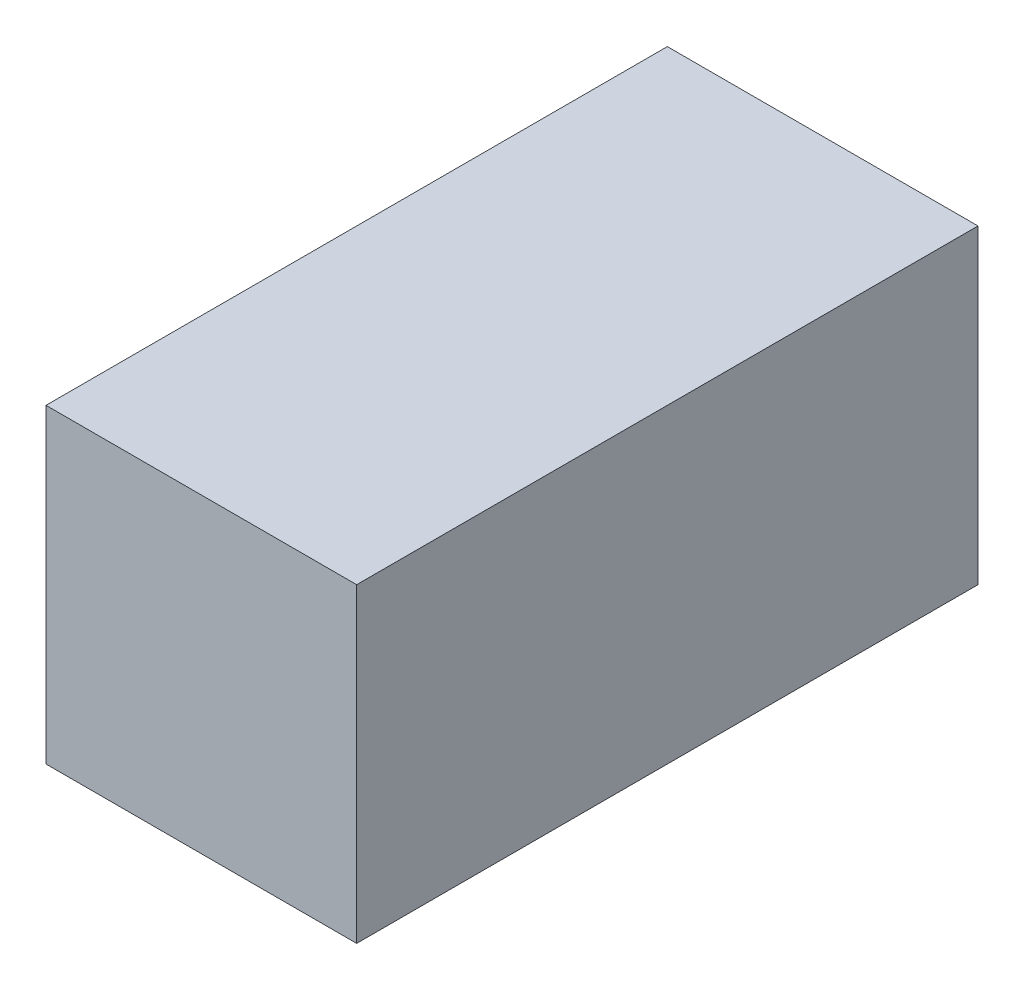
SolidWorks part; units mm, degrees
material "Custom Plastic"
ref_plane "Front Plane" through (0, 0, 0) normal (0, 0, 1) x (1, 0, 0)
ref_plane "Top Plane" through (0, 0, 0) normal (0, 1, 0) x (1, 0, 0)
ref_plane "Right Plane" through (0, 0, 0) normal (1, 0, 0) x (0, 0, -1)
sketch "Compressor Cross Section" plane through (0, 0, 0) normal (0, 0, 1) x (1, 0, 0)
  line L1 (-63.5, -63.5) -> (63.5, -63.5)
  line L2 (-63.5, -63.5) -> (-63.5, 63.5)
  line L3 (-63.5, 63.5) -> (63.5, 63.5)
  line L4 (63.5, -63.5) -> (63.5, 63.5)
  line L5 (-63.5, -63.5) -> (63.5, 63.5) construction
  line L6 (-63.5, 63.5) -> (63.5, -63.5) construction
  point P0 (0, 0)
  dimension "D1" = 127
  dimension "D2" = 127
extrude "Air Compressor" add sketch "Compressor Cross Section" along normal mid plane 254
